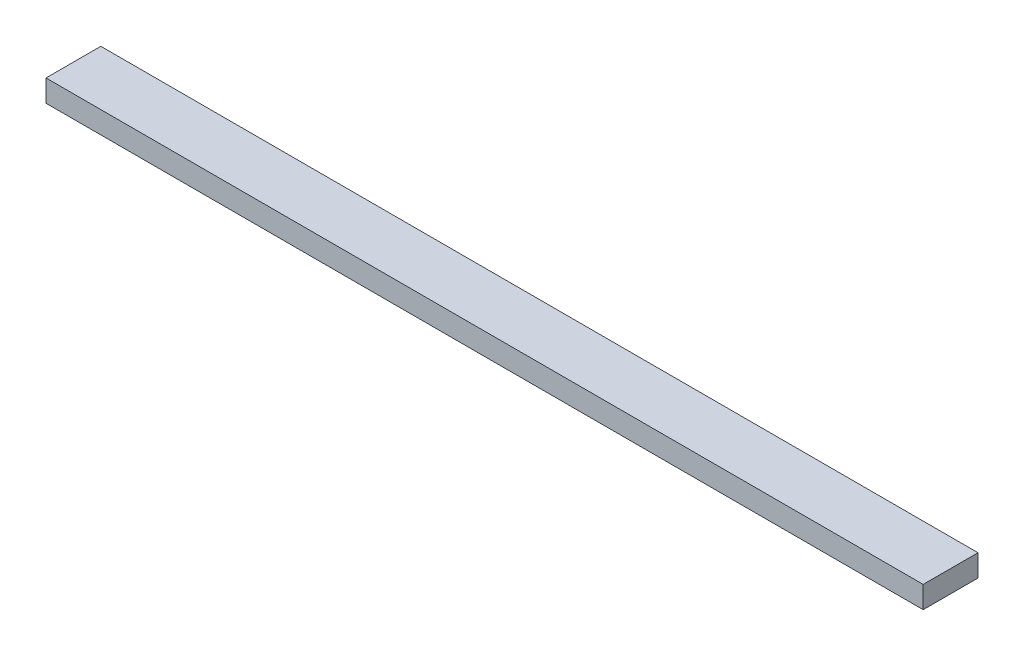
SolidWorks part; units mm, degrees
ref_plane "Спереди" through (0, 0, 0) normal (0, 0, 1) x (1, 0, 0)
ref_plane "Сверху" through (0, 0, 0) normal (0, 1, 0) x (1, 0, 0)
ref_plane "Справа" through (0, 0, 0) normal (1, 0, 0) x (0, 0, -1)
sketch "Эскиз1" plane through (0, 0, 0) normal (1, 0, 0) x (0, 0, -1)
  line L1 (0, 0) -> (25, 0)
  line L2 (0, 0) -> (0, 10)
  line L3 (0, 10) -> (25, 10)
  line L4 (25, 0) -> (25, 10)
extrude "Бобышка-Вытянуть1" add sketch "Эскиз1" along normal blind 400
